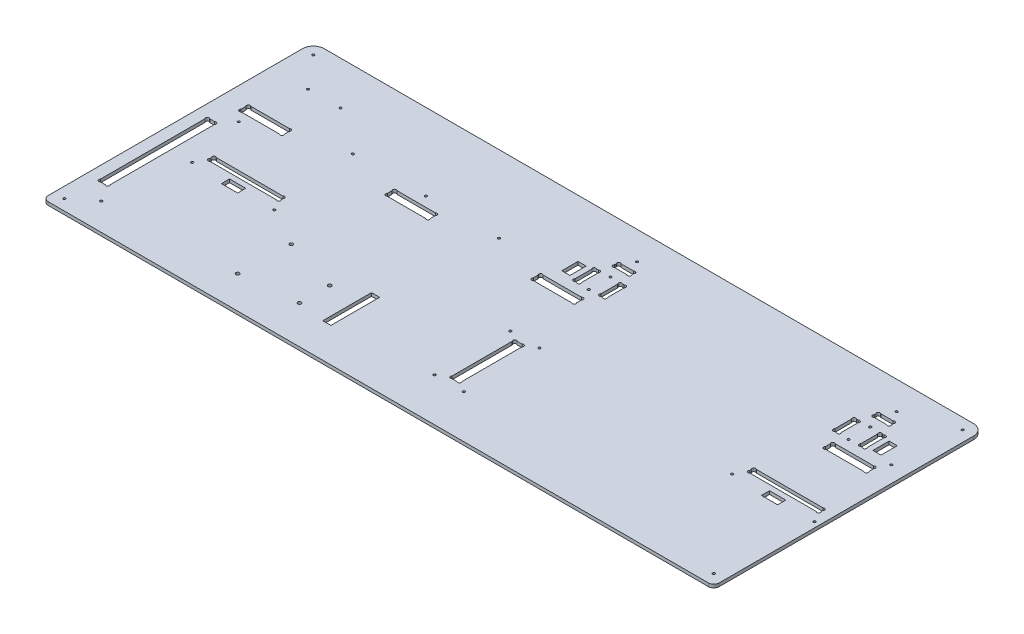
SolidWorks part; units mm, degrees
other "Marquage1"
sketch "Esquisse8" plane through (0, 3, 0) normal (-0.3047, 0.6733, 0.6737) x (0.9431, 0.1142, 0.3123)
ref_plane "Plan de face" through (0, 0, 0) normal (0, 0, 1) x (1, 0, 0)
ref_plane "Plan de dessus" through (0, 0, 0) normal (0, 1, 0) x (1, 0, 0)
ref_plane "Plan de droite" through (0, 0, 0) normal (1, 0, 0) x (0, 0, -1)
sketch "Esquisse1" plane through (0, 0, 0) normal (0, 1, 0) x (1, 0, 0)
  line L26 (317, 211.2627) -> (317, 212.7373)
  line L28 (319.2627, 215) -> (330.7373, 215)
  line L29 (333, 211.2627) -> (333, 212.7373)
  line L30 (330.7373, 209) -> (319.2627, 209)
  line L31 (312.2627, 179.5) -> (313.7373, 179.5)
  line L32 (312.2627, 199.5) -> (313.7373, 199.5)
  line L33 (310, 197.2373) -> (310, 181.7627)
  line L34 (316, 181.7627) -> (316, 197.2373)
  line L35 (334, 181.7627) -> (334, 197.2373)
  line L36 (340, 197.2373) -> (340, 181.7627)
  line L37 (337.7373, 199.5) -> (336.2627, 199.5)
  line L38 (337.7373, 179.5) -> (336.2627, 179.5)
  line L39 (552.2627, 179.5) -> (553.7373, 179.5)
  line L40 (552.2627, 199.5) -> (553.7373, 199.5)
  line L41 (550, 197.2373) -> (550, 181.7627)
  line L42 (556, 181.7627) -> (556, 197.2373)
  line L43 (574, 181.7627) -> (574, 197.2373)
  line L44 (580, 197.2373) -> (580, 181.7627)
  line L45 (577.7373, 199.5) -> (576.2627, 199.5)
  line L46 (577.7373, 179.5) -> (576.2627, 179.5)
  line L47 (559.2627, 209) -> (570.7373, 209)
  line L48 (557, 211.2627) -> (557, 212.7373)
  line L49 (570.7373, 215) -> (559.2627, 215)
  line L50 (573, 211.2627) -> (573, 212.7373)
  line L55 (560, 167.7373) -> (560, 163.2627)
  line L56 (600, 167.7373) -> (600, 163.2627)
  line L57 (562.2627, 170) -> (597.7373, 170)
  line L58 (597.7373, 161) -> (562.2627, 161)
  line L59 (292.2627, 161) -> (327.7373, 161)
  line L60 (327.7373, 170) -> (292.2627, 170)
  line L61 (290, 167.7373) -> (290, 163.2627)
  line L62 (330, 167.7373) -> (330, 163.2627)
  line L64 (20, 167.7373) -> (20, 163.2627)
  line L65 (60, 167.7373) -> (60, 163.2627)
  line L66 (22.2627, 170) -> (57.7373, 170)
  line L67 (57.7373, 161) -> (22.2627, 161)
  line L70 (155, 167.7373) -> (155, 163.2627)
  line L71 (195, 167.7373) -> (195, 163.2627)
  line L72 (157.2627, 170) -> (192.7373, 170)
  line L73 (192.7373, 161) -> (157.2627, 161)
  line L76 (10, 250) -> (610, 250)
  line L77 (0, 240) -> (0, 0)
  line L78 (0, 0) -> (620, 0)
  line L79 (620, 240) -> (620, 0)
  line L84 (13.2627, 40) -> (17.7373, 40)
  line L85 (13.2627, 141) -> (17.7373, 141)
  line L86 (11, 138.7373) -> (11, 42.2627)
  line L87 (20, 42.2627) -> (20, 138.7373)
  line L98 (337.7373, 45) -> (333.2627, 45)
  line L99 (337.7373, 105) -> (333.2627, 105)
  line L100 (340, 47.2627) -> (340, 102.7373)
  line L101 (331, 102.7373) -> (331, 47.2627)
  line L109 (610, 109.2627) -> (610, 110.7373)
  line L110 (544, 109.2627) -> (544, 110.7373)
  line L111 (607.7373, 107) -> (546.2627, 107)
  line L112 (546.2627, 113) -> (607.7373, 113)
  line L113 (108.7373, 113) -> (47.2627, 113)
  line L114 (47.2627, 107) -> (108.7373, 107)
  line L115 (111, 109.2627) -> (111, 110.7373)
  line L116 (45, 109.2627) -> (45, 110.7373)
  arc A0 (319.2627, 215) -> (317, 212.7373) centre (318.1314, 213.8686) ccw
  arc A1 (319.2627, 209) -> (317, 211.2627) centre (318.1314, 210.1314) cw
  arc A2 (330.7373, 209) -> (333, 211.2627) centre (331.8686, 210.1314) ccw
  arc A3 (330.7373, 215) -> (333, 212.7373) centre (331.8686, 213.8686) cw
  arc A4 (313.7373, 179.5) -> (316, 181.7627) centre (314.8686, 180.6314) ccw
  arc A5 (312.2627, 179.5) -> (310, 181.7627) centre (311.1314, 180.6314) cw
  arc A6 (312.2627, 199.5) -> (310, 197.2373) centre (311.1314, 198.3686) ccw
  arc A7 (313.7373, 199.5) -> (316, 197.2373) centre (314.8686, 198.3686) cw
  arc A8 (336.2627, 179.5) -> (334, 181.7627) centre (335.1314, 180.6314) cw
  arc A9 (336.2627, 199.5) -> (334, 197.2373) centre (335.1314, 198.3686) ccw
  arc A10 (337.7373, 199.5) -> (340, 197.2373) centre (338.8686, 198.3686) cw
  arc A11 (337.7373, 179.5) -> (340, 181.7627) centre (338.8686, 180.6314) ccw
  arc A12 (552.2627, 179.5) -> (550, 181.7627) centre (551.1314, 180.6314) cw
  arc A13 (552.2627, 199.5) -> (550, 197.2373) centre (551.1314, 198.3686) ccw
  arc A14 (553.7373, 199.5) -> (556, 197.2373) centre (554.8686, 198.3686) cw
  arc A15 (553.7373, 179.5) -> (556, 181.7627) centre (554.8686, 180.6314) ccw
  arc A16 (576.2627, 199.5) -> (574, 197.2373) centre (575.1314, 198.3686) ccw
  arc A17 (577.7373, 199.5) -> (580, 197.2373) centre (578.8686, 198.3686) cw
  arc A18 (577.7373, 179.5) -> (580, 181.7627) centre (578.8686, 180.6314) ccw
  arc A19 (576.2627, 179.5) -> (574, 181.7627) centre (575.1314, 180.6314) cw
  arc A20 (559.2627, 215) -> (557, 212.7373) centre (558.1314, 213.8686) ccw
  arc A21 (559.2627, 209) -> (557, 211.2627) centre (558.1314, 210.1314) cw
  arc A22 (570.7373, 209) -> (573, 211.2627) centre (571.8686, 210.1314) ccw
  arc A23 (570.7373, 215) -> (573, 212.7373) centre (571.8686, 213.8686) cw
  arc A29 (560, 163.2627) -> (562.2627, 161) centre (561.1314, 162.1314) ccw
  arc A30 (560, 167.7373) -> (562.2627, 170) centre (561.1314, 168.8686) cw
  arc A31 (600, 167.7373) -> (597.7373, 170) centre (598.8686, 168.8686) ccw
  arc A32 (600, 163.2627) -> (597.7373, 161) centre (598.8686, 162.1314) cw
  arc A34 (290, 163.2627) -> (292.2627, 161) centre (291.1314, 162.1314) ccw
  arc A35 (290, 167.7373) -> (292.2627, 170) centre (291.1314, 168.8686) cw
  arc A36 (330, 167.7373) -> (327.7373, 170) centre (328.8686, 168.8686) ccw
  arc A37 (330, 163.2627) -> (327.7373, 161) centre (328.8686, 162.1314) cw
  arc A40 (20, 163.2627) -> (22.2627, 161) centre (21.1314, 162.1314) ccw
  arc A41 (20, 167.7373) -> (22.2627, 170) centre (21.1314, 168.8686) cw
  arc A42 (60, 167.7373) -> (57.7373, 170) centre (58.8686, 168.8686) ccw
  arc A43 (60, 163.2627) -> (57.7373, 161) centre (58.8686, 162.1314) cw
  arc A44 (155, 163.2627) -> (157.2627, 161) centre (156.1314, 162.1314) ccw
  arc A45 (155, 167.7373) -> (157.2627, 170) centre (156.1314, 168.8686) cw
  arc A46 (195, 163.2627) -> (192.7373, 161) centre (193.8686, 162.1314) cw
  arc A47 (195, 167.7373) -> (192.7373, 170) centre (193.8686, 168.8686) ccw
  arc A50 (17.7373, 40) -> (20, 42.2627) centre (18.8686, 41.1314) ccw
  arc A52 (13.2627, 40) -> (11, 42.2627) centre (12.1314, 41.1314) cw
  arc A53 (17.7373, 141) -> (20, 138.7373) centre (18.8686, 139.8686) cw
  arc A54 (13.2627, 141) -> (11, 138.7373) centre (12.1314, 139.8686) ccw
  arc A56 (10, 250) -> (0, 240) centre (10, 240) ccw
  arc A57 (610, 250) -> (620, 240) centre (610, 240) cw
  arc A59 (331, 47.2627) -> (333.2627, 45) centre (332.1314, 46.1314) ccw
  arc A60 (340, 47.2627) -> (337.7373, 45) centre (338.8686, 46.1314) cw
  arc A61 (331, 102.7373) -> (333.2627, 105) centre (332.1314, 103.8686) cw
  arc A62 (340, 102.7373) -> (337.7373, 105) centre (338.8686, 103.8686) ccw
  arc A64 (607.7373, 107) -> (610, 109.2627) centre (608.8686, 108.1314) ccw
  circle A65 centre (539, 98) radius 1.1
  arc A66 (607.7373, 113) -> (610, 110.7373) centre (608.8686, 111.8686) cw
  circle A67 centre (615, 98) radius 1.1
  arc A68 (546.2627, 113) -> (544, 110.7373) centre (545.1314, 111.8686) ccw
  arc A69 (546.2627, 107) -> (544, 109.2627) centre (545.1314, 108.1314) cw
  arc A70 (108.7373, 107) -> (111, 109.2627) centre (109.8686, 108.1314) ccw
  arc A71 (108.7373, 113) -> (111, 110.7373) centre (109.8686, 111.8686) cw
  arc A73 (47.2627, 113) -> (45, 110.7373) centre (46.1314, 111.8686) ccw
  arc A75 (47.2627, 107) -> (45, 109.2627) centre (46.1314, 108.1314) cw
  point P1 (337, 199.5)
  point P7 (340, 189.5)
  dimension "D25" = 6
  dimension "D28" = 16
  dimension "D29" = 20
  dimension "D32" = 9.5
  dimension "D33" = 35
  dimension "D39" = 10
  dimension "D49" = 1.1314
  dimension "D57" = 6
  dimension "D55" = 10
  dimension "D62" = 5
  dimension "D63" = 1.6
  dimension "D64" = 9
  dimension "D65" = 1.1314
  dimension "D66" = 1.1314
  dimension "D67" = 620
  dimension "D9" = 2.2627
  dimension "D10" = 1.6
  dimension "D78" = 3.7373
  dimension "D14" = 1.6
  dimension "D36" = 1.6
  dimension "D61" = 1.6
  dimension "D95" = 1.6
  dimension "D107" = 1.6
  dimension "D118" = 1.6
  dimension "D119" = 1.6
  dimension "D128" = 6
  dimension "D141" = 1.6
  dimension "D58" = 2.2
  dimension "D2" = 250
  dimension "D8" = 20
  dimension "D13" = 40
  dimension "D16" = 1.1314
  dimension "D17" = 1.1314
  dimension "D19" = 2.2627
  dimension "D20" = 2.2627
  dimension "D21" = 80
  dimension "D22" = 9
  dimension "D23" = 1.1314
  dimension "D24" = 1.1314
  dimension "D26" = 6
  dimension "D27" = 6
  dimension "D30" = 40
  dimension "D31" = 18
  dimension "D37" = 1.1314
  dimension "D38" = 2.2627
  dimension "D40" = 1.1314
  dimension "D41" = 1.1314
  dimension "D42" = 1.1314
  dimension "D43" = 1.1314
  dimension "D45" = 1
  dimension "D46" = 1.1314
  dimension "D47" = 1.1314
  dimension "D48" = 1.1314
  dimension "D51" = 3.7373
  dimension "D52" = 66
  dimension "D53" = 10
  dimension "D54" = 66
  dimension "D56" = 107
  dimension "D59" = 1.1314
  dimension "D60" = 2.2627
  dimension "D68" = 60
  dimension "D70" = 6
  dimension "D72" = 1.1314
  dimension "D73" = 1.1314
  dimension "D74" = 63.7373
  dimension "D75" = 2.2627
  dimension "D76" = 2.2627
  dimension "D77" = 45
  dimension "D79" = 45
  dimension "D83" = 280
  dimension "D84" = 1.1314
  dimension "D85" = 1.1314
  dimension "D86" = 1.1314
  dimension "D87" = 1.1314
  dimension "D88" = 9
  dimension "D89" = 101
  dimension "D90" = 40
  dimension "D91" = 11
  dimension "D96" = 1.1314
  dimension "D97" = 1.1314
  dimension "D98" = 1.1314
  dimension "D100" = 1.1314
  dimension "D105" = 9
  dimension "D106" = 40
  dimension "D108" = 20
  dimension "D109" = 80
  dimension "D110" = 1.1314
  dimension "D111" = 1.1314
  dimension "D112" = 1.1314
  dimension "D113" = 1.1314
  dimension "D114" = 40
  dimension "D115" = 95
  dimension "D116" = 95
  dimension "D117" = 40
  dimension "D120" = 1.1314
  dimension "D121" = 1.1314
  dimension "D122" = 1.1314
  dimension "D123" = 1.1314
  dimension "D124" = 1.1314
  dimension "D125" = 1.1314
  dimension "D126" = 1.1314
  dimension "D127" = 1.1314
  dimension "D129" = 6
  dimension "D130" = 6
  dimension "D132" = 20
  dimension "D133" = 16
  dimension "D135" = 35
  dimension "D136" = 9.5
  dimension "D139" = 1
  dimension "D140" = 18
  dimension "D142" = 1.1314
  dimension "D143" = 1.1314
  dimension "D144" = 1.1314
  dimension "D145" = 1.1314
  dimension "D146" = 1.1314
  dimension "D147" = 1.1314
  dimension "D148" = 1.1314
  dimension "D149" = 1.1314
  dimension "D150" = 1.1314
  dimension "D151" = 1.1314
  dimension "D152" = 1.1314
  dimension "D153" = 1.1314
  dimension "D154" = 9
  dimension "D155" = 5
extrude "Extrusion1" add sketch "Esquisse1" along normal blind 3
sketch "Esquisse2" plane through (0, 3, 0) normal (0, 1, 0) x (-1, 0, 0)
  line L0 (-610, -250) -> (-10, -250) construction
  line L5 (-620, 21.4973) -> (-620, -261.3021) construction
  line L7 (-573, -142.8) -> (-72, -142.8)
  line L8 (-573, -142.8) -> (-573, -147)
  line L9 (-573, -147) -> (-72, -147)
  line L10 (-72, -142.8) -> (-72, -147)
  dimension "D1" = 47
  dimension "D2" = 4.2
  dimension "D3" = 501
  dimension "D4" = 103
extrude "Enlèv. mat.-Extru.1" [suppressed] cut sketch "Esquisse2" against normal through all
sketch "Esquisse3" plane through (0, 3, 0) normal (0, 1, 0) x (1, 0, 0)
  line L0 (574, 197.2373) -> (574, 181.7627) construction
  line L1 (556, 181.7627) -> (556, 197.2373) construction
  line L2 (559.2627, 209) -> (570.7373, 209) construction
  line L4 (576.2627, 179.5) -> (577.7373, 179.5) construction
  line L5 (577.7373, 199.5) -> (576.2627, 199.5) construction
  line L6 (334, 197.2373) -> (334, 181.7627) construction
  circle A0 centre (565, 179.5) radius 1.1
  circle A1 centre (565, 199.5) radius 1.1
  circle A2 centre (325, 179.5) radius 1.1
  circle A3 centre (325, 199.5) radius 1.1
  dimension "D1" = 2.2
  dimension "D2" = 9
  dimension "D3" = 9
  dimension "D4" = 20
  dimension "D5" = 9.5
  dimension "D6" = 0
  dimension "D7" = 0
  dimension "D8" = 9
extrude "Enlèv. mat.-Extru.2" cut sketch "Esquisse3" against normal through all
fillet "Congé1" radius 5 2 edges at (620, 1.5, 0) (0, 1.5, 0)
sketch "Esquisse4" plane through (0, 0, 0) normal (0, -1, 0) x (1, 0, 0)
  line L0 (0, -240) -> (0, -5) construction
  line L1 (5, 0) -> (615, 0) construction
  line L2 (610, -250) -> (10, -250) construction
  line L3 (620, -5) -> (620, -240) construction
  circle A0 centre (10, -10) radius 1.1
  circle A1 centre (610, -10) radius 1.1
  circle A2 centre (610, -240) radius 1.1
  circle A3 centre (10, -240) radius 1.1
  dimension "D1" = 2.2
  dimension "D2" = 10
  dimension "D3" = 10
  dimension "D4" = 10
  dimension "D5" = 10
  dimension "D6" = 10
  dimension "D7" = 10
  dimension "D8" = 10
  dimension "D9" = 10
extrude "Enlèv. mat.-Extru.3" cut sketch "Esquisse4" against normal through all
sketch "Esquisse5" plane through (0, 3, 0) normal (0, 1, 0) x (1, 0, 0)
  line L1 (0, 240) -> (0, 5) construction
  line L2 (5, 0) -> (615, 0) construction
  circle A0 centre (151.27, 78.26) radius 1.59
  circle A1 centre (150, 30) radius 1.59
  circle A2 centre (202.07, 63.02) radius 1.59
  circle A3 centre (202.07, 35.08) radius 1.59
  dimension "D1" = 3.18
  dimension "D7" = 30
  dimension "D2" = 48.26
  dimension "D3" = 27.94
  dimension "D4" = 52.07
  dimension "D5" = 5.08
  dimension "D6" = 150
  dimension "D8" = 1.27
extrude "Enlèv. mat.-Extru.4" cut sketch "Esquisse5" against normal through all
sketch "Esquisse6" plane through (0, 3, 0) normal (0, 1, 0) x (1, 0, 0)
  line L0 (544, 110.7373) -> (544, 109.2627) construction
  line L1 (569.5, 102) -> (584.5, 102)
  line L2 (569.5, 102) -> (569.5, 94.5)
  line L3 (569.5, 94.5) -> (584.5, 94.5)
  line L4 (584.5, 102) -> (584.5, 94.5)
  line L5 (610, 109.2627) -> (610, 110.7373) construction
  line L6 (546.2627, 107) -> (607.7373, 107) construction
  line L8 (585, 197) -> (592.5, 197)
  line L9 (585, 197) -> (585, 182)
  line L10 (585, 182) -> (592.5, 182)
  line L11 (592.5, 197) -> (592.5, 182)
  line L12 (305, 197) -> (297.5, 197)
  line L13 (305, 197) -> (305, 182)
  line L14 (305, 182) -> (297.5, 182)
  line L15 (297.5, 197) -> (297.5, 182)
  line L16 (577.7373, 199.5) -> (576.2627, 199.5) construction
  line L17 (576.2627, 179.5) -> (577.7373, 179.5) construction
  line L18 (580, 181.7627) -> (580, 197.2373) construction
  line L19 (310, 197.2373) -> (310, 181.7627) construction
  line L20 (313.7373, 199.5) -> (312.2627, 199.5) construction
  line L21 (45, 110.7373) -> (45, 109.2627) construction
  line L22 (227.07, 76.63) -> (234.57, 76.63)
  line L23 (227.07, 76.63) -> (227.07, 31.63)
  line L24 (227.07, 31.63) -> (234.57, 31.63)
  line L25 (234.57, 76.63) -> (234.57, 31.63)
  line L26 (70.5, 102) -> (85.5, 102)
  line L27 (70.5, 102) -> (70.5, 94.5)
  line L28 (70.5, 94.5) -> (85.5, 94.5)
  line L29 (85.5, 102) -> (85.5, 94.5)
  circle A0 centre (150, 30) radius 1.59 construction
  circle A1 centre (151.27, 78.26) radius 1.59 construction
  circle A2 centre (202.07, 63.02) radius 1.59 construction
  dimension "D1" = 15
  dimension "D2" = 7.5
  dimension "D3" = 25.5
  dimension "D4" = 25.5
  dimension "D5" = 5
  dimension "D6" = 7.5
  dimension "D7" = 15
  dimension "D8" = 15
  dimension "D9" = 7.5
  dimension "D10" = 2.5
  dimension "D11" = 2.5
  dimension "D12" = 5
  dimension "D13" = 5
  dimension "D14" = 2.5
  dimension "D15" = 7.5
  dimension "D16" = 45
  dimension "D17" = 1.63
  dimension "D18" = 1.63
  dimension "D19" = 25
  dimension "D20" = 15
  dimension "D21" = 25.5
extrude "Enlèv. mat.-Extru.5" cut sketch "Esquisse6" against normal through all
sketch "Esquisse7" plane through (0, 3, 0) normal (0, 1, 0) x (1, 0, 0)
  line L0 (610, 250) -> (10, 250) construction
  line L1 (5, 0) -> (615, 0) construction
  line L2 (331, 102.7373) -> (331, 47.2627) construction
  line L3 (340, 47.2627) -> (340, 102.7373) construction
  line L4 (570.7373, 215) -> (559.2627, 215) construction
  line L5 (330.7373, 215) -> (319.2627, 215) construction
  line L6 (597.7373, 170) -> (562.2627, 170) construction
  line L7 (192.7373, 170) -> (157.2627, 170) construction
  line L8 (0, 240) -> (0, 5) construction
  line L10 (47.2627, 107) -> (108.7373, 107) construction
  line L11 (45, 110.7373) -> (45, 109.2627) construction
  line L12 (111, 109.2627) -> (111, 110.7373) construction
  circle A0 centre (349, 110) radius 1.1
  circle A1 centre (349, 40) radius 1.1
  circle A2 centre (322, 110) radius 1.1
  circle A3 centre (322, 40) radius 1.1
  circle A4 centre (605, 179) radius 1.1
  circle A5 centre (565, 224) radius 1.1
  circle A6 centre (325, 224) radius 1.1
  circle A7 centre (175, 179) radius 1.1
  circle A8 centre (242.5, 179) radius 1.1
  circle A9 centre (107.5, 179) radius 1.1
  circle A10 centre (116, 98) radius 1.1
  circle A11 centre (40, 98) radius 1.1
  circle A12 centre (29, 152) radius 1.1
  circle A13 centre (29, 25) radius 1.1
  circle A14 centre (35, 210) radius 1.1
  circle A15 centre (65, 210) radius 1.1
  point P34 (325, 215)
  point P38 (565, 215)
  point P47 (175, 170)
  point P59 (0, 0)
  dimension "D1" = 2.2
  dimension "D2" = 40
  dimension "D3" = 9
  dimension "D4" = 9
  dimension "D5" = 70
  dimension "D6" = 9
  dimension "D7" = 40
  dimension "D8" = 9
  dimension "D9" = 9
  dimension "D10" = 67.5
  dimension "D11" = 67.5
  dimension "D12" = 127
  dimension "D13" = 25
  dimension "D14" = 29
  dimension "D15" = 9
  dimension "D16" = 5
  dimension "D17" = 5
  dimension "D18" = 35
  dimension "D19" = 40
  dimension "D20" = 30
extrude "Enlèv. mat.-Extru.6" cut sketch "Esquisse7" against normal through all
